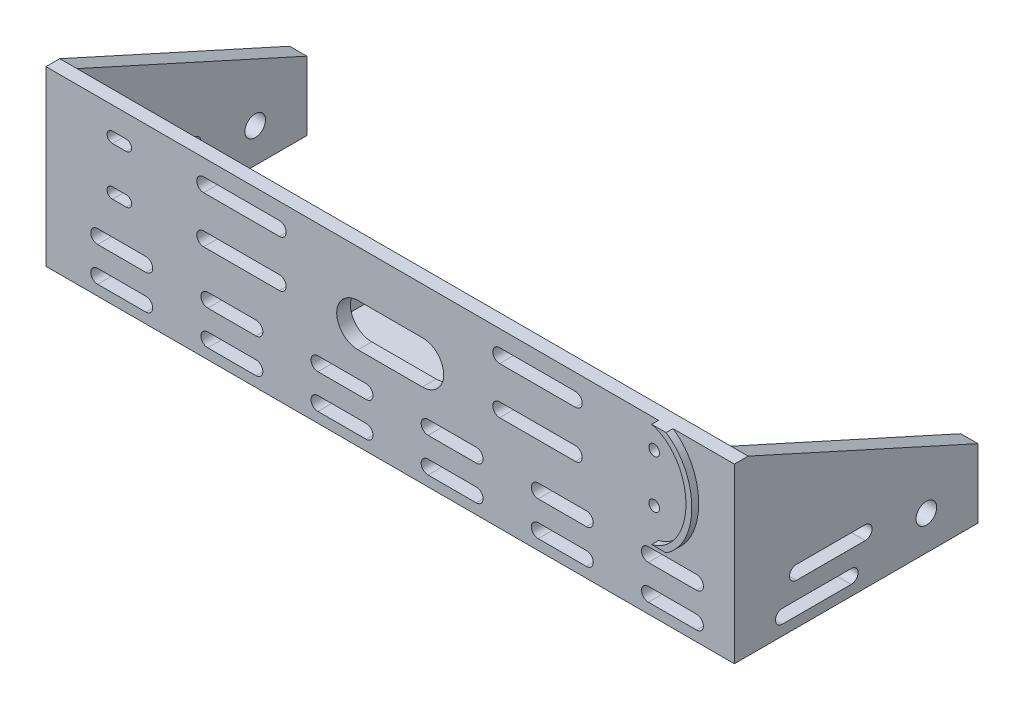
SolidWorks part; units mm, degrees
ref_plane "前视基准面" through (0, 0, 0) normal (0, 0, 1) x (1, 0, 0)
ref_plane "上视基准面" through (0, 0, 0) normal (0, 1, 0) x (1, 0, 0)
ref_plane "右视基准面" through (0, 0, 0) normal (1, 0, 0) x (0, 0, -1)
sketch "草图1" plane through (0, 0, 0) normal (0, 0, 1) x (1, 0, 0)
  line L1 (-100, 100) -> (100, 100)
  line L2 (-100, 100) -> (-100, -100)
  line L3 (-100, -100) -> (100, -100)
  line L4 (100, 100) -> (100, -100)
  line L5 (-100, 100) -> (100, -100) construction
  line L6 (-100, -100) -> (100, 100) construction
  point P0 (0, 0)
extrude "凸台-拉伸1" add sketch "草图1" along normal blind 4
sketch "草图2" plane through (0, 0, 4) normal (0, 0, 1) x (1, 0, 0)
  line L2 (-72.6076, -10.5305) -> (78.3924, -10.5305)
  line L3 (-72.6076, 19.72) -> (78.3924, 19.72)
  line L12 (100, -100) -> (100, 100)
  line L13 (100, 100) -> (-100, 100)
  line L14 (-100, 100) -> (-100, -100)
  line L15 (-100, -100) -> (100, -100)
  line L16 (100, -100) -> (100, 100)
  line L17 (100, 100) -> (-100, 100)
  line L18 (-100, 100) -> (-100, -100)
  line L19 (-100, -100) -> (100, -100)
  spline S4 degree 3 number of poles 131 (78.3924, -10.5305) -> (78.3924, 19.72)
  spline S6 degree 3 number of poles 138 (-72.6076, 19.72) -> (-72.6076, -10.5305)
  dimension "D1" = 0
extrude "切除-拉伸1" cut sketch "草图2" against normal blind 10
sketch "草图3" plane through (0, 0, 0) normal (0, 0, -1) x (-1, 0, 0)
  line L5 (-12.2424, -6.2053) -> (6.4576, -6.2053)
  line L6 (6.4576, 6.1947) -> (-12.2424, 6.1947)
  arc A6 (6.4576, -6.2053) -> (6.4576, 6.1947) centre (6.4576, -0.0053) ccw
  arc A7 (-12.2424, 6.1947) -> (-12.2424, -6.2053) centre (-12.2424, -0.0053) ccw
extrude "切除-拉伸2" cut sketch "草图3" against normal blind 10
sketch "草图4" plane through (0, 0, 0) normal (0, 0, -1) x (-1, 0, 0)
  circle A1 centre (-79.5924, 11.5947) radius 1.2645
  circle A3 centre (-79.5924, -2.4053) radius 1.2645
  circle A5 centre (73.8076, 11.5947) radius 1.2645
  circle A7 centre (73.8076, -2.4053) radius 1.2645
extrude "切除-拉伸3" cut sketch "草图4" against normal blind 10
sketch "草图5" plane through (0, 0, 0) normal (0, 0, -1) x (-1, 0, 0)
  circle A4 centre (73.8076, -2.4053) radius 1.2645 construction
  circle A5 centre (73.8076, -2.4053) radius 1.2645
  circle A6 centre (73.8076, 11.5947) radius 1.2645 construction
  circle A7 centre (73.8076, 11.5947) radius 1.2645
  circle A8 centre (73.8076, 11.5947) radius 1.5645
  circle A9 centre (73.8076, -2.4053) radius 1.5645
  circle A10 centre (-79.5924, -2.4053) radius 1.5645
  circle A11 centre (-79.5924, 11.5947) radius 1.5645
  dimension "D1" = 0.3
extrude "切除-拉伸4" cut sketch "草图5" against normal blind 10
sketch "草图6" plane through (0, 0, 0) normal (0, 0, -1) x (-1, 0, 0)
  line L0 (-78.3924, -10.5305) -> (-78.3924, -7.5305)
  line L1 (72.6076, -10.5305) -> (-78.3924, -10.5305) construction
  line L2 (-78.3924, -7.5305) -> (72.6076, -7.5305)
  line L3 (72.6076, -7.5305) -> (72.6076, -10.5305)
  line L4 (72.6076, -10.5305) -> (-78.3924, -10.5305)
  spline S0 degree 3 number of poles 138 (72.6076, 19.72) -> (72.6076, -10.5305) construction
extrude "凸台-拉伸2" add sketch "草图6" along normal blind 25
sketch "草图7" plane through (0, -7.5305, 0) normal (0, 1, 0) x (1, 0, 0)
  line L0 (23.6853, 0) -> (25.6853, 0)
  line L1 (-72.6076, 25) -> (78.3924, 25) construction
  line L2 (-72.6076, 0) -> (78.3924, 0) construction
  line L3 (67.6853, 25) -> (67.6853, 0)
  line L4 (69.6853, 25) -> (69.6853, 0)
  line L5 (67.6853, 0) -> (69.6853, 0)
  line L6 (67.6853, 25) -> (69.6853, 25)
  line L7 (25.6853, 25) -> (25.6853, 0)
  line L8 (23.6853, 25) -> (25.6853, 25)
  line L9 (23.6853, 25) -> (23.6853, 0)
  line L10 (-20.3147, 0) -> (-18.3147, 0)
  line L11 (-18.3147, 25) -> (-18.3147, 0)
  line L12 (-20.3147, 25) -> (-18.3147, 25)
  line L13 (-20.3147, 25) -> (-20.3147, 0)
  line L14 (-64.3147, 0) -> (-62.3147, 0)
  line L15 (-62.3147, 25) -> (-62.3147, 0)
  line L16 (-64.3147, 25) -> (-62.3147, 25)
  line L17 (-64.3147, 25) -> (-64.3147, 0)
  dimension "D1" = 4
extrude "凸台-拉伸3" add sketch "草图7" along normal up to surface (27.2505 mm away) contours L5 L4 L6 L3 | L0 L7 L8 L9 | L10 L11 L12 L13 | L14 L15 L16 L17 up to face at (2.8924, 19.72, 2)
sketch "草图8" plane through (69.6853, 0, 0) normal (1, 0, 0) x (0, 0, -1)
  line L0 (0, 19.72) -> (25, -7.5305)
  line L1 (25, 19.72) -> (25, -7.5305) construction
  line L2 (25, -7.5305) -> (25, 19.72)
  line L3 (25, 19.72) -> (0, 19.72) construction
  line L4 (25, 19.72) -> (0, 19.72)
extrude "切除-拉伸5" cut sketch "草图8" against normal through all
sketch "草图9" plane through (78.3924, 0, 0) normal (1, 0, 0) x (0, 0, -1)
  line L4 (0, -7.5305) -> (0, -10.5305)
  line L5 (0, -10.5305) -> (25, -10.5305)
  line L6 (25, -10.5305) -> (25, -7.5305)
  line L7 (25, -7.5305) -> (0, -7.5305)
  line L8 (0, -7.5305) -> (0, -10.5305)
  line L9 (0, -10.5305) -> (25, -10.5305)
  line L10 (25, -10.5305) -> (25, -7.5305)
  line L11 (25, -7.5305) -> (0, -7.5305)
  dimension "D1" = 0
extrude "凸台-拉伸4" add sketch "草图9" along normal blind 19.5
sketch "草图10" plane through (-72.6076, 0, 0) normal (-1, 0, 0) x (0, 0, 1)
  line L4 (0, -10.5305) -> (0, -7.5305)
  line L5 (0, -7.5305) -> (-25, -7.5305)
  line L6 (-25, -7.5305) -> (-25, -10.5305)
  line L7 (-25, -10.5305) -> (0, -10.5305)
  line L8 (0, -10.5305) -> (0, -7.5305)
  line L9 (0, -7.5305) -> (-25, -7.5305)
  line L10 (-25, -7.5305) -> (-25, -10.5305)
  line L11 (-25, -10.5305) -> (0, -10.5305)
  dimension "D1" = 0
extrude "凸台-拉伸5" add sketch "草图10" along normal blind 19.5
sketch "草图11" plane through (0, 0, 0) normal (0, 0, -1) x (-1, 0, 0)
  line L3 (-85.6613, -7.5305) -> (-69.6853, -7.5305)
  line L4 (-69.6853, -7.5305) -> (-69.6853, 19.72)
  line L5 (-69.6853, 19.72) -> (-78.3924, 19.72)
  line L6 (-85.6613, -7.5305) -> (-69.6853, -7.5305)
  line L7 (-69.6853, -7.5305) -> (-69.6853, 19.72)
  line L8 (-69.6853, 19.72) -> (-78.3924, 19.72)
  line L9 (64.3147, -7.5305) -> (79.8759, -7.5305)
  line L10 (72.6076, 19.72) -> (64.3147, 19.72)
  line L11 (64.3147, 19.72) -> (64.3147, -7.5305)
  line L12 (64.3147, -7.5305) -> (79.8759, -7.5305)
  line L13 (72.6076, 19.72) -> (64.3147, 19.72)
  line L14 (64.3147, 19.72) -> (64.3147, -7.5305)
  line L16 (72.6076, 19.72) -> (92.1076, 19.72)
  line L17 (92.1076, 19.72) -> (92.1076, -7.5305)
  line L18 (-97.8924, -7.5305) -> (-97.8924, 19.72)
  line L19 (-97.8924, 19.72) -> (-78.3924, 19.72)
  line L20 (92.1076, -10.5305) -> (72.6076, -10.5305) construction
  line L21 (92.1076, -10.5305) -> (72.6076, -10.5305)
  line L22 (92.1076, -10.5305) -> (92.1076, -7.5305) construction
  line L23 (92.1076, -10.5305) -> (92.1076, -7.5305)
  line L24 (-97.8924, -10.5305) -> (-78.3924, -10.5305) construction
  line L25 (-97.8924, -10.5305) -> (-78.3924, -10.5305)
  line L26 (-97.8924, -7.5305) -> (-97.8924, -10.5305) construction
  line L27 (-97.8924, -7.5305) -> (-97.8924, -10.5305)
  circle A0 centre (-79.5924, 11.5947) radius 1.5645 construction
  circle A1 centre (-79.5924, 11.5947) radius 1.5645
  circle A2 centre (-79.5924, -2.4053) radius 1.5645 construction
  circle A3 centre (-79.5924, -2.4053) radius 1.5645
  circle A4 centre (73.8076, 11.5947) radius 1.5645 construction
  circle A5 centre (73.8076, 11.5947) radius 1.5645
  circle A6 centre (73.8076, -2.4053) radius 1.5645 construction
  circle A7 centre (73.8076, -2.4053) radius 1.5645
  spline S0 degree 3 poles (-1964.2663, -2201.2134) (52.8845, 109.7009) (102.2719, 11.1981) (79.208, -8.1129) (78.9676, -8.2994) (78.6552, -8.5321) (78.2893, -8.7882) (77.9099, -9.0221) (77.6333, -9.182) (77.5386, -9.2349) (77.2976, -9.3648) (76.9963, -9.5185) (76.6866, -9.6585) (76.3996, -9.7797) (76.1261, -9.889) (75.7015, -10.0382) (75.4033, -10.1279) (75.1767, -10.1905) (75.0211, -10.2315) (74.7914, -10.2863) (74.561, -10.3356) (74.3307, -10.3792) (74.0991, -10.4175) (73.8974, -10.446) (73.6934, -10.4708) (73.4878, -10.4919) (73.2229, -10.5125) (72.9576, -10.5256) (72.7484, -10.5299) (72.6472, -10.5304) (72.6264, -10.5305) (71.9929, -10.5316) (65.2261, -10.4746) (3070.0625, -10.2829) knots -0.052986 -0.052986 -0.052986 -0.052986 0.035105 0.035549 0.036008 0.036008 0.03671 0.037341 0.037341 0.037666 0.037666 0.038159 0.038675 0.038675 0.039081 0.039546 0.040009 0.040009 0.040249 0.0405 0.040755 0.04101 0.041263 0.041513 0.041655 0.041897 0.042132 0.042414 0.042612 0.04266 0.04266 0.042662 0.044149 0.044149 0.044149 0.044149 weights 1 1 1 1 1 1 1 1 1 1 1 1 1 1 1 1 1 1 1 1 1 1 1 1 1 1 1 1 1 1 1 1 1 1 only from (79.8759, -7.5305) to (72.6076, -10.5305) construction
  spline S1 degree 3 number of poles 100 (-78.3924, 19.72) -> (-85.6613, -7.5305)
  spline S2 degree 3 poles (79.8759, -7.5305) (79.7709, -7.6281) (79.5523, -7.8246) (79.208, -8.1129) (78.9676, -8.2994) (78.6552, -8.5321) (78.2893, -8.7882) (77.9099, -9.0221) (77.6333, -9.182) (77.5386, -9.2349) (77.2976, -9.3648) (76.9963, -9.5185) (76.6866, -9.6585) (76.3996, -9.7797) (76.1261, -9.889) (75.7015, -10.0382) (75.4033, -10.1279) (75.1767, -10.1905) (75.0211, -10.2315) (74.7914, -10.2863) (74.561, -10.3356) (74.3307, -10.3792) (74.0991, -10.4175) (73.8974, -10.446) (73.6934, -10.4708) (73.4878, -10.4919) (73.2229, -10.5125) (72.9576, -10.5256) (72.7484, -10.5299) (72.6472, -10.5304) (72.6264, -10.5305) (72.6196, -10.5305) (72.6122, -10.5305) (72.6076, -10.5305) knots 0.034679 0.034679 0.034679 0.034679 0.035105 0.035549 0.036008 0.036008 0.03671 0.037341 0.037341 0.037666 0.037666 0.038159 0.038675 0.038675 0.039081 0.039546 0.040009 0.040009 0.040249 0.0405 0.040755 0.04101 0.041263 0.041513 0.041655 0.041897 0.042132 0.042414 0.042612 0.04266 0.04266 0.042662 0.042676 0.042676 0.042676 0.042676 weights 1 1 1 1 1 1 1 1 1 1 1 1 1 1 1 1 1 1 1 1 1 1 1 1 1 1 1 1 1 1 1 1 1 1
  spline S3 degree 3 number of poles 107 (79.8759, -7.5305) -> (72.6076, 19.72)
  spline S4 degree 3 poles (-3072.7814, -10.217) (-88.9792, -10.474) (-77.7118, -10.5313) (-78.4074, -10.5305) (-78.4599, -10.5304) (-78.5623, -10.5294) (-78.7097, -10.5257) (-78.8675, -10.5194) (-79.0115, -10.5113) (-79.1631, -10.5005) (-79.3142, -10.4875) (-79.4815, -10.4703) (-79.6251, -10.4531) (-79.7145, -10.4411) (-79.8286, -10.4253) (-80.0633, -10.3896) (-80.448, -10.3171) (-80.8046, -10.2327) (-81.0101, -10.1772) (-81.2711, -10.1043) (-81.6531, -9.9845) (-82.205, -9.7759) (-82.7332, -9.5427) (-83.0804, -9.3664) (-83.3635, -9.2127) (-83.5947, -9.0822) (-83.9446, -8.8678) (-84.3033, -8.629) (-84.5366, -8.4609) (-84.6781, -8.355) (-84.8686, -8.2112) (-133.4278, 30.7748) (133.5555, 417.232) (-2378.5676, -1932.7537) knots -0.001469 -0.001469 -0.001469 -0.001469 0.000004 0.000016 0.000016 0.000132 0.000273 0.000411 0.000581 0.000707 0.000886 0.001066 0.001245 0.001336 0.001336 0.001585 0.002038 0.002493 0.002673 0.002673 0.003304 0.003874 0.004447 0.005039 0.005039 0.005408 0.005829 0.006254 0.006682 0.006682 0.00678 0.007394 0.192748 0.192748 0.192748 0.192748 weights 1 1 1 1 1 1 1 1 1 1 1 1 1 1 1 1 1 1 1 1 1 1 1 1 1 1 1 1 1 1 1 1 1 1 only from (-78.3924, -10.5305) to (-85.6613, -7.5305) construction
  spline S5 degree 3 poles (-78.3924, -10.5305) (-78.3939, -10.5305) (-78.4, -10.5305) (-78.4074, -10.5305) (-78.4599, -10.5304) (-78.5623, -10.5294) (-78.7097, -10.5257) (-78.8675, -10.5194) (-79.0115, -10.5113) (-79.1631, -10.5005) (-79.3142, -10.4875) (-79.4815, -10.4703) (-79.6251, -10.4531) (-79.7145, -10.4411) (-79.8286, -10.4253) (-80.0633, -10.3896) (-80.448, -10.3171) (-80.8046, -10.2327) (-81.0101, -10.1772) (-81.2711, -10.1043) (-81.6531, -9.9845) (-82.205, -9.7759) (-82.7332, -9.5427) (-83.0804, -9.3664) (-83.3635, -9.2127) (-83.5947, -9.0822) (-83.9446, -8.8678) (-84.3033, -8.629) (-84.5366, -8.4609) (-84.6781, -8.355) (-84.8686, -8.2112) (-85.211, -7.9363) (-85.5144, -7.6671) (-85.6613, -7.5305) knots 0 0 0 0 0.000004 0.000016 0.000016 0.000132 0.000273 0.000411 0.000581 0.000707 0.000886 0.001066 0.001245 0.001336 0.001336 0.001585 0.002038 0.002493 0.002673 0.002673 0.003304 0.003874 0.004447 0.005039 0.005039 0.005408 0.005829 0.006254 0.006682 0.006682 0.00678 0.007394 0.007994 0.007994 0.007994 0.007994 weights 1 1 1 1 1 1 1 1 1 1 1 1 1 1 1 1 1 1 1 1 1 1 1 1 1 1 1 1 1 1 1 1 1 1
  dimension "D1" = 0
  dimension "D2" = 0
extrude "凸台-拉伸7" add sketch "草图11" against normal up to surface (4 mm away) up to face at (81.1569, 11.5947, 4)
sketch "草图12" plane through (97.8924, 0, 0) normal (1, 0, 0) x (0, 0, -1)
  line L0 (0, 19.72) -> (0, -7.5305)
  line L1 (0, 19.72) -> (0, -7.5305) construction
  line L2 (-4, 19.72) -> (0, 19.72) construction
  line L3 (25, -7.5305) -> (0, -7.5305) construction
  line L4 (0, -7.5305) -> (25, -7.5305)
  line L5 (25, -7.5305) -> (25, 19.72)
  line L6 (25, 19.72) -> (0, 19.72)
extrude "凸台-拉伸8" add sketch "草图12" against normal blind 2
sketch "草图13" plane through (-92.1076, 0, 0) normal (-1, 0, 0) x (0, 0, 1)
  line L0 (-25, -7.5305) -> (0, -7.5305)
  line L1 (0, -7.5305) -> (-25, -7.5305) construction
  line L2 (0, -7.5305) -> (0, 19.72) construction
  line L3 (0, -7.5305) -> (0, 19.72)
  line L4 (4, 19.72) -> (0, 19.72) construction
  line L5 (0, 19.72) -> (-25, 19.72)
  line L6 (-25, 19.72) -> (-25, -7.5305)
extrude "凸台-拉伸9" add sketch "草图13" against normal blind 2
sketch "草图14" plane through (97.8924, 0, 0) normal (1, 0, 0) x (0, 0, -1)
  line L0 (0, 19.72) -> (25, -7.5305) construction
  line L1 (0, 19.72) -> (25, -7.5305)
  line L2 (-4, 19.72) -> (25, 19.72) construction
  line L3 (0, 19.72) -> (25, 19.72)
  line L4 (25, -10.5305) -> (25, 19.72) construction
  line L5 (25, -7.5305) -> (25, 19.72)
extrude "切除-拉伸6" cut sketch "草图14" against normal through all
sketch "草图15" plane through (0, 0, 4) normal (0, 0, 1) x (1, 0, 0)
  line L1 (97.8924, 19.72) -> (-92.1076, 19.72) construction
  line L3 (-79.2671, 19.72) -> (-75.0584, 19.72)
  line L6 (2.8924, 19.72) -> (2.8924, 11.147) construction
  line L7 (80.8432, -10.5305) -> (85.0515, -10.5305)
  line L10 (-92.1076, -10.5305) -> (97.8924, -10.5305) construction
  line L11 (-79.2668, -10.5305) -> (-75.0584, -10.5305)
  line L15 (85.0518, 19.72) -> (80.8432, 19.72)
  spline S0 degree 3 poles (85.0518, 19.72) (85.1632, 19.6484) (85.4315, 19.4703) (86.1206, 18.9769) (87.4522, 17.859) (89.1534, 15.8951) (90.6757, 13.2854) (92.1095, 9.5189) (92.7901, 4.6117) (91.9718, -1.3231) (89.8146, -5.9461) (87.3308, -8.8099) (85.859, -9.9966) (85.1617, -10.4597) (85.0515, -10.5305) knots 0.005857 0.005857 0.005857 0.005857 0.006191 0.006668 0.008002 0.010669 0.013336 0.016003 0.021338 0.026672 0.032007 0.034674 0.036473 0.036807 0.036807 0.036807 0.036807
  spline S1 degree 3 poles (-75.0584, 19.72) (-75.1603, 19.6948) (-75.7066, 19.5507) (-76.6676, 19.2127) (-77.8948, 18.5992) (-79.0593, 17.8276) (-80.4578, 16.6538) (-82.5778, 14.2113) (-84.5252, 10.0319) (-85.2857, 4.6081) (-84.5294, -0.8444) (-82.5636, -5.0408) (-80.1537, -7.815) (-78.2999, -9.2065) (-76.6615, -10.0277) (-75.6724, -10.3713) (-75.1497, -10.508) (-75.0584, -10.5305) knots 0.002364 0.002364 0.002364 0.002364 0.002667 0.004001 0.005334 0.006668 0.008002 0.010669 0.016003 0.021338 0.026672 0.032007 0.034674 0.037341 0.038675 0.040009 0.040293 0.040293 0.040293 0.040293
  spline S2 degree 3 poles (80.8432, 19.72) (80.9451, 19.6948) (81.4914, 19.5507) (82.4524, 19.2127) (83.6795, 18.5992) (84.844, 17.8276) (86.2425, 16.6538) (88.3625, 14.2113) (90.3099, 10.0319) (91.0705, 4.6081) (90.3141, -0.8444) (88.3483, -5.0408) (85.9384, -7.815) (84.0847, -9.2065) (82.4463, -10.0277) (81.4571, -10.3713) (80.9345, -10.508) (80.8432, -10.5305) knots 0.002364 0.002364 0.002364 0.002364 0.002667 0.004001 0.005334 0.006668 0.008002 0.010669 0.016003 0.021338 0.026672 0.032007 0.034674 0.037341 0.038675 0.040009 0.040293 0.040293 0.040293 0.040293
  spline S7 degree 3 poles (-79.2671, 19.72) (-79.3785, 19.6484) (-79.6467, 19.4703) (-80.3358, 18.9769) (-81.6674, 17.859) (-83.3686, 15.8951) (-84.891, 13.2854) (-86.3248, 9.5189) (-87.0054, 4.6117) (-86.1871, -1.3231) (-84.0298, -5.9461) (-81.5461, -8.8099) (-80.0742, -9.9966) (-79.3769, -10.4597) (-79.2668, -10.5305) knots 0.005857 0.005857 0.005857 0.005857 0.006191 0.006668 0.008002 0.010669 0.013336 0.016003 0.021338 0.026672 0.032007 0.034674 0.036473 0.036807 0.036807 0.036807 0.036807
extrude "凸台-拉伸10" add sketch "草图15" along normal blind 2
sketch "草图17" plane through (97.8924, 0, 0) normal (1, 0, 0) x (0, 0, -1)
  line L1 (66.7816, -30.5305) -> (66.7816, -10.5305)
  line L2 (25, -10.5305) -> (66.7816, -10.5305)
  line L3 (-4, -10.5305) -> (25, -10.5305) construction
  line L4 (-4, 19.72) -> (-4, -10.5305) construction
  line L5 (-4, -10.5305) -> (-4, -30.5305)
  line L6 (-4, -30.5305) -> (66.7816, -30.5305)
  line L12 (25, -7.5305) -> (0, 19.72)
  line L13 (0, 19.72) -> (-4, 19.72)
  line L14 (-4, 19.72) -> (-4, -10.5305)
  line L15 (-4, -10.5305) -> (25, -10.5305)
  line L16 (25, -10.5305) -> (25, -7.5305)
  line L17 (25, -7.5305) -> (0, 19.72)
  line L18 (0, 19.72) -> (-4, 19.72)
  line L19 (-4, 19.72) -> (-4, -10.5305)
  line L21 (25, -10.5305) -> (25, -7.5305)
  dimension "D1" = 0
extrude "凸台-拉伸11" add sketch "草图17" along normal blind 5
sketch "草图18" plane through (102.8924, 0, 0) normal (1, 0, 0) x (0, 0, -1)
  line L1 (36.7816, -30.5305) -> (36.7816, -10.5305) construction
  line L2 (66.7816, -10.5305) -> (25, -10.5305) construction
  line L3 (66.7816, -10.5305) -> (36.7816, -10.5305) construction
  line L4 (66.7816, -10.5305) -> (66.7816, -30.5305) construction
  line L5 (66.7816, -30.5305) -> (36.7816, -30.5305) construction
  line L6 (-4, -30.5305) -> (66.7816, -30.5305) construction
  line L7 (36.7816, -20.5305) -> (66.7816, -20.5305) construction
  circle A0 centre (51.7816, -20.5305) radius 3
extrude "切除-拉伸7" cut sketch "草图18" against normal through all
ref_plane "基准面1" through (2.8924, 0, 0) normal (-1, 0, 0) x (0, 0, 1)
mirror "镜向1" about plane through (2.8924, 0, 0) normal (-1, 0, 0) of "凸台-拉伸11", "切除-拉伸7"
sketch "草图19" plane through (102.8924, 0, 0) normal (1, 0, 0) x (0, 0, -1)
  line L0 (0, 19.72) -> (66.7816, -10.5305)
  line L1 (66.7816, -10.5305) -> (25, -10.5305)
  line L2 (25, -10.5305) -> (25, -7.5305)
  line L3 (25, -10.5305) -> (25, -7.5305) construction
  line L4 (25, -7.5305) -> (0, 19.72) construction
  line L5 (25, -7.5305) -> (0, 19.72)
extrude "凸台-拉伸12" add sketch "草图19" against normal up to surface (5 mm away) up to face at (97.8924, -20.5305, -54.7816)
sketch "草图20" plane through (-97.1076, 0, 0) normal (-1, 0, 0) x (0, 0, 1)
  line L0 (-66.7816, -10.5305) -> (0, 19.72)
  line L1 (0, 19.72) -> (-25, -7.5305)
  line L2 (-25, -7.5305) -> (-25, -10.5305)
  line L3 (-25, -10.5305) -> (-25, -7.5305) construction
  line L4 (-66.7816, -10.5305) -> (-25, -10.5305) construction
  line L5 (-25, -10.5305) -> (-66.7816, -10.5305)
extrude "凸台-拉伸13" add sketch "草图20" against normal up to surface (5 mm away) up to face at (-92.1076, -20.5305, -48.7816)
sketch "草图21" plane through (0, 0, 0) normal (0, 0, -1) x (-1, 0, 0)
  line L0 (-67.6853, 6.0947) -> (-23.6853, 6.0947) construction
  line L1 (-67.6853, 19.72) -> (-67.6853, -7.5305) construction
  line L2 (-23.6853, 19.72) -> (-23.6853, -7.5305) construction
  line L3 (-45.6853, 6.0947) -> (-45.6853, 19.72) construction
  line L4 (-67.6853, 19.72) -> (-25.6853, 19.72) construction
  line L5 (-45.6853, 12.9074) -> (-67.6853, 12.9074) construction
  line L6 (-56.6853, 12.9074) -> (-34.6853, 12.9074) construction
  line L7 (-23.6853, 19.72) -> (18.3147, 19.72) construction
  line L8 (-56.6853, 14.9074) -> (-34.6853, 14.9074)
  line L9 (-56.6853, 10.9074) -> (-34.6853, 10.9074)
  line L10 (-23.6853, 19.72) -> (18.3147, 19.72) construction
  line L11 (-2.6853, 19.72) -> (-2.6853, 9.3359) construction
  line L12 (-56.6853, -0.7179) -> (-34.6853, -0.7179) construction
  line L13 (-56.6853, -2.7179) -> (-34.6853, -2.7179)
  line L14 (-56.6853, 1.2821) -> (-34.6853, 1.2821)
  line L15 (51.3147, -0.7179) -> (29.3147, -0.7179) construction
  line L16 (51.3147, -2.7179) -> (29.3147, -2.7179)
  line L17 (51.3147, 1.2821) -> (29.3147, 1.2821)
  line L18 (51.3147, 12.9074) -> (29.3147, 12.9074) construction
  line L19 (51.3147, 14.9074) -> (29.3147, 14.9074)
  line L20 (51.3147, 10.9074) -> (29.3147, 10.9074)
  arc A0 (-56.6853, 14.9074) -> (-56.6853, 10.9074) centre (-56.6853, 12.9074) ccw
  arc A1 (-34.6853, 10.9074) -> (-34.6853, 14.9074) centre (-34.6853, 12.9074) ccw
  arc A2 (-56.6853, -2.7179) -> (-56.6853, 1.2821) centre (-56.6853, -0.7179) cw
  arc A3 (-34.6853, 1.2821) -> (-34.6853, -2.7179) centre (-34.6853, -0.7179) cw
  arc A4 (51.3147, -2.7179) -> (51.3147, 1.2821) centre (51.3147, -0.7179) ccw
  arc A5 (29.3147, 1.2821) -> (29.3147, -2.7179) centre (29.3147, -0.7179) ccw
  arc A6 (51.3147, 14.9074) -> (51.3147, 10.9074) centre (51.3147, 12.9074) cw
  arc A7 (29.3147, 10.9074) -> (29.3147, 14.9074) centre (29.3147, 12.9074) cw
  point P16 (-45.6853, 12.9074)
  point P25 (-45.6853, -0.7179)
  point P32 (40.3147, -0.7179)
  point P39 (40.3147, 12.9074)
extrude "切除-拉伸8" cut sketch "草图21" against normal blind 4
sketch "草图22" plane through (102.8924, 0, 0) normal (1, 0, 0) x (0, 0, -1)
  line L0 (23.8908, -20.5305) -> (-4, -20.5305) construction
  line L1 (-4, 19.72) -> (-4, -30.5305) construction
  line L2 (23.8908, -20.5305) -> (23.8908, -30.5305) construction
  line L3 (-4, -30.5305) -> (66.7816, -30.5305) construction
  line L4 (9.9454, -20.5305) -> (9.9454, -30.5305) construction
  line L5 (9.9454, -25.5305) -> (29.9454, -25.5305) construction
  line L6 (19.9454, -25.5305) -> (33.3908, 4.5947) construction
  line L7 (9.9454, -23.5305) -> (29.9454, -23.5305)
  line L8 (9.9454, -27.5305) -> (29.9454, -27.5305)
  line L9 (66.7816, -10.5305) -> (0, 19.72) construction
  line L10 (9.9454, -25.5305) -> (25.2598, 8.2779) construction
  line L11 (29.9454, -25.5305) -> (41.8547, 0.7608) construction
  line L12 (14.0175, -16.5408) -> (34.0175, -16.5408) construction
  line L13 (14.0175, -14.5408) -> (34.0175, -14.5408)
  line L14 (14.0175, -18.5408) -> (34.0175, -18.5408)
  arc A0 (9.9454, -23.5305) -> (9.9454, -27.5305) centre (9.9454, -25.5305) ccw
  arc A1 (29.9454, -27.5305) -> (29.9454, -23.5305) centre (29.9454, -25.5305) ccw
  arc A2 (14.0175, -14.5408) -> (14.0175, -18.5408) centre (14.0175, -16.5408) ccw
  arc A3 (34.0175, -18.5408) -> (34.0175, -14.5408) centre (34.0175, -16.5408) ccw
  point P14 (19.9454, -25.5305)
  point P26 (24.0175, -16.5408)
extrude "切除-拉伸9" cut sketch "草图22" against normal through all
sketch "草图23" plane through (97.8924, 0, 0) normal (-1, 0, 0) x (0, 0, 1)
  line L0 (4, -30.5305) -> (0, -30.5305)
  line L1 (4, -30.5305) -> (-66.7816, -30.5305) construction
  line L2 (0, -30.5305) -> (0, -10.5305)
  line L3 (4, -10.5305) -> (-25, -10.5305) construction
  line L4 (0, -10.5305) -> (4, -10.5305)
  line L5 (4, -10.5305) -> (4, -30.5305)
extrude "凸台-拉伸14" add sketch "草图23" along normal up to surface (190 mm away)
sketch "草图24" plane through (0, 0, 4) normal (0, 0, 1) x (1, 0, 0)
  line L0 (-82.1076, -25.5305) -> (-68.1076, -25.5305) construction
  line L2 (-92.1076, -20.5305) -> (-92.1076, -30.5305) construction
  line L3 (102.8924, -30.5305) -> (-97.1076, -30.5305) construction
  line L4 (-92.1076, -30.5305) -> (97.8924, -30.5305) construction
  line L5 (97.8924, -30.5305) -> (97.8924, -20.5305) construction
  line L6 (-92.1076, -20.5305) -> (97.8924, -20.5305) construction
  line L7 (-92.1076, -25.5305) -> (-82.1076, -25.5305) construction
  line L8 (-82.1076, -15.5305) -> (-68.1076, -15.5305) construction
  line L9 (-82.1076, -23.5305) -> (-68.1076, -23.5305)
  line L10 (-82.1076, -27.5305) -> (-68.1076, -27.5305)
  line L11 (-82.1076, -17.5305) -> (-68.1076, -17.5305)
  line L12 (-82.1076, -13.5305) -> (-68.1076, -13.5305)
  line L13 (-50.1076, -25.5305) -> (-36.1076, -25.5305) construction
  line L14 (-50.1076, -23.5305) -> (-36.1076, -23.5305)
  line L15 (-50.1076, -27.5305) -> (-36.1076, -27.5305)
  line L16 (-50.1076, -15.5305) -> (-36.1076, -15.5305) construction
  line L17 (-50.1076, -17.5305) -> (-36.1076, -17.5305)
  line L18 (-50.1076, -13.5305) -> (-36.1076, -13.5305)
  line L19 (-18.1076, -25.5305) -> (-4.1076, -25.5305) construction
  line L20 (-18.1076, -23.5305) -> (-4.1076, -23.5305)
  line L21 (-18.1076, -27.5305) -> (-4.1076, -27.5305)
  line L22 (-18.1076, -15.5305) -> (-4.1076, -15.5305) construction
  line L23 (-18.1076, -17.5305) -> (-4.1076, -17.5305)
  line L24 (-18.1076, -13.5305) -> (-4.1076, -13.5305)
  line L25 (13.8924, -25.5305) -> (27.8924, -25.5305) construction
  line L26 (13.8924, -23.5305) -> (27.8924, -23.5305)
  line L27 (13.8924, -27.5305) -> (27.8924, -27.5305)
  line L28 (13.8924, -15.5305) -> (27.8924, -15.5305) construction
  line L29 (13.8924, -17.5305) -> (27.8924, -17.5305)
  line L30 (13.8924, -13.5305) -> (27.8924, -13.5305)
  line L31 (45.8924, -25.5305) -> (59.8924, -25.5305) construction
  line L32 (45.8924, -23.5305) -> (59.8924, -23.5305)
  line L33 (45.8924, -27.5305) -> (59.8924, -27.5305)
  line L34 (45.8924, -15.5305) -> (59.8924, -15.5305) construction
  line L35 (45.8924, -17.5305) -> (59.8924, -17.5305)
  line L36 (45.8924, -13.5305) -> (59.8924, -13.5305)
  line L37 (77.8924, -25.5305) -> (91.8924, -25.5305) construction
  line L38 (77.8924, -23.5305) -> (91.8924, -23.5305)
  line L39 (77.8924, -27.5305) -> (91.8924, -27.5305)
  line L40 (77.8924, -15.5305) -> (91.8924, -15.5305) construction
  line L41 (77.8924, -17.5305) -> (91.8924, -17.5305)
  line L42 (77.8924, -13.5305) -> (91.8924, -13.5305)
  arc A0 (-82.1076, -23.5305) -> (-82.1076, -27.5305) centre (-82.1076, -25.5305) ccw
  arc A1 (-68.1076, -27.5305) -> (-68.1076, -23.5305) centre (-68.1076, -25.5305) ccw
  arc A2 (-82.1076, -17.5305) -> (-82.1076, -13.5305) centre (-82.1076, -15.5305) cw
  arc A3 (-68.1076, -13.5305) -> (-68.1076, -17.5305) centre (-68.1076, -15.5305) cw
  arc A4 (-50.1076, -23.5305) -> (-50.1076, -27.5305) centre (-50.1076, -25.5305) ccw
  arc A5 (-36.1076, -27.5305) -> (-36.1076, -23.5305) centre (-36.1076, -25.5305) ccw
  arc A6 (-50.1076, -17.5305) -> (-50.1076, -13.5305) centre (-50.1076, -15.5305) cw
  arc A7 (-36.1076, -13.5305) -> (-36.1076, -17.5305) centre (-36.1076, -15.5305) cw
  arc A8 (-18.1076, -23.5305) -> (-18.1076, -27.5305) centre (-18.1076, -25.5305) ccw
  arc A9 (-4.1076, -27.5305) -> (-4.1076, -23.5305) centre (-4.1076, -25.5305) ccw
  arc A10 (-18.1076, -17.5305) -> (-18.1076, -13.5305) centre (-18.1076, -15.5305) cw
  arc A11 (-4.1076, -13.5305) -> (-4.1076, -17.5305) centre (-4.1076, -15.5305) cw
  arc A12 (13.8924, -23.5305) -> (13.8924, -27.5305) centre (13.8924, -25.5305) ccw
  arc A13 (27.8924, -27.5305) -> (27.8924, -23.5305) centre (27.8924, -25.5305) ccw
  arc A14 (13.8924, -17.5305) -> (13.8924, -13.5305) centre (13.8924, -15.5305) cw
  arc A15 (27.8924, -13.5305) -> (27.8924, -17.5305) centre (27.8924, -15.5305) cw
  arc A16 (45.8924, -23.5305) -> (45.8924, -27.5305) centre (45.8924, -25.5305) ccw
  arc A17 (59.8924, -27.5305) -> (59.8924, -23.5305) centre (59.8924, -25.5305) ccw
  arc A18 (45.8924, -17.5305) -> (45.8924, -13.5305) centre (45.8924, -15.5305) cw
  arc A19 (59.8924, -13.5305) -> (59.8924, -17.5305) centre (59.8924, -15.5305) cw
  arc A20 (77.8924, -23.5305) -> (77.8924, -27.5305) centre (77.8924, -25.5305) ccw
  arc A21 (91.8924, -27.5305) -> (91.8924, -23.5305) centre (91.8924, -25.5305) ccw
  arc A22 (77.8924, -17.5305) -> (77.8924, -13.5305) centre (77.8924, -15.5305) cw
  arc A23 (91.8924, -13.5305) -> (91.8924, -17.5305) centre (91.8924, -15.5305) cw
  point P11 (-75.1076, -25.5305)
  point P16 (-75.1076, -15.5305)
  point P27 (-43.1076, -25.5305)
  point P32 (-43.1076, -15.5305)
  point P41 (-11.1076, -25.5305)
  point P46 (-11.1076, -15.5305)
  point P55 (20.8924, -25.5305)
  point P60 (20.8924, -15.5305)
  point P69 (52.8924, -25.5305)
  point P74 (52.8924, -15.5305)
  point P83 (84.8924, -25.5305)
  point P88 (84.8924, -15.5305)
  dimension "D1" = 6
extrude "切除-拉伸10" cut sketch "草图24" against normal blind 4 contours L11 A3 L12 A2 | L17 A7 L18 A6 | L10 A1 L9 A0 | L14 A5 L15 A4 | L20 A9 L21 A8 | L23 A11 L24 A10 | L29 A15 L30 A14 | L26 A13 L27 A12 | L32 A17 L33 A16 | L35 A19 L36 A18 | L38 A21 L39 A20 | L41 A23 L42 A22
sketch "草图25" plane through (0, 0, 4) normal (0, 0, 1) x (1, 0, 0)
  line L0 (-73.8076, 11.5947) -> (-77.8076, 11.5947) construction
  line L1 (-77.8076, 11.5947) -> (-75.6442, -0.8405) construction
  line L2 (-75.3721, -2.4053) -> (-77.8077, -2.4053) construction
  line L3 (-75.0584, 19.72) -> (-79.2671, 19.72)
  line L4 (-79.2668, -10.5305) -> (-75.0584, -10.5305)
  line L5 (-75.0584, 19.72) -> (-79.2671, 19.72)
  line L6 (-79.2668, -10.5305) -> (-75.0584, -10.5305)
  line L7 (-77.8077, -0.8403) -> (-73.8076, -0.8408)
  line L8 (-77.8077, -3.9702) -> (-73.8076, -3.9698)
  line L9 (-77.8076, 13.1597) -> (-73.8076, 13.1592)
  line L10 (-77.8076, 10.0297) -> (-73.8076, 10.0302)
  arc A1 (-77.8074, 13.1597) -> (-77.5394, 10.0529) centre (-77.8076, 11.5947) ccw
  circle A2 centre (-73.8076, -2.4053) radius 1.5645 construction
  arc A3 (-77.8075, -0.8403) -> (-77.8073, -3.9702) centre (-77.8077, -2.4053) ccw
  arc A4 (-73.8076, -3.9698) -> (-73.8076, -0.8408) centre (-73.8076, -2.4053) ccw
  circle A5 centre (-73.8076, 11.5947) radius 1.5645 construction
  arc A6 (-73.8076, 10.0302) -> (-73.8076, 13.1592) centre (-73.8076, 11.5947) ccw
  spline S2 degree 3 poles (-2514.7242, -3179.0871) (-79.2912, 140.8799) (-44.8804, -21.0685) (-76.6615, -10.0277) (-78.2999, -9.2065) (-80.1537, -7.815) (-82.5636, -5.0408) (-84.5294, -0.8444) (-85.2857, 4.6081) (-84.5252, 10.0319) (-82.5778, 14.2113) (-80.4578, 16.6538) (-79.0593, 17.8276) (-77.8948, 18.5992) (-76.6676, 19.2127) (-49.0329, 28.9324) (22.5212, -72.8615) (3852.9028, -731.526) knots -0.089529 -0.089529 -0.089529 -0.089529 0.002649 0.003983 0.005316 0.007984 0.010651 0.015985 0.02132 0.026654 0.031989 0.034656 0.03599 0.037323 0.038657 0.03999 0.122736 0.122736 0.122736 0.122736 only from (-75.0584, -10.5305) to (-75.0584, 19.72)
  spline S3 degree 3 poles (-2923.4646, -2788.7941) (57.4892, -33.7904) (-52.8144, 38.6831) (-80.3358, 18.9769) (-81.6674, 17.859) (-83.3686, 15.8951) (-84.891, 13.2854) (-86.3248, 9.5189) (-87.0054, 4.6117) (-86.1871, -1.3231) (-84.0298, -5.9461) (-81.5461, -8.8099) (-42.3822, -40.3881) (145.0739, 149.5546) (3878.31, -559.4752) knots -0.077645 -0.077645 -0.077645 -0.077645 0.006191 0.006668 0.008002 0.010669 0.013336 0.016003 0.021338 0.026672 0.032007 0.034674 0.036473 0.159721 0.159721 0.159721 0.159721 only from (-79.2671, 19.72) to (-79.2668, -10.5305)
  spline S4 degree 3 poles (-75.0584, -10.5305) (-75.1497, -10.508) (-75.6724, -10.3713) (-76.6615, -10.0277) (-78.2999, -9.2065) (-80.1537, -7.815) (-82.5636, -5.0408) (-84.5294, -0.8444) (-85.2857, 4.6081) (-84.5252, 10.0319) (-82.5778, 14.2113) (-80.4578, 16.6538) (-79.0593, 17.8276) (-77.8948, 18.5992) (-76.6676, 19.2127) (-75.7066, 19.5507) (-75.1603, 19.6948) (-75.0584, 19.72) knots 0.002364 0.002364 0.002364 0.002364 0.002649 0.003983 0.005316 0.007984 0.010651 0.015985 0.02132 0.026654 0.031989 0.034656 0.03599 0.037323 0.038657 0.03999 0.040293 0.040293 0.040293 0.040293
  spline S5 degree 3 poles (-79.2671, 19.72) (-79.3785, 19.6484) (-79.6467, 19.4703) (-80.3358, 18.9769) (-81.6674, 17.859) (-83.3686, 15.8951) (-84.891, 13.2854) (-86.3248, 9.5189) (-87.0054, 4.6117) (-86.1871, -1.3231) (-84.0298, -5.9461) (-81.5461, -8.8099) (-80.0742, -9.9966) (-79.3769, -10.4597) (-79.2668, -10.5305) knots 0.005857 0.005857 0.005857 0.005857 0.006191 0.006668 0.008002 0.010669 0.013336 0.016003 0.021338 0.026672 0.032007 0.034674 0.036473 0.036807 0.036807 0.036807 0.036807
  dimension "D1" = 0
extrude "切除-拉伸11" cut sketch "草图25" against normal blind 10
sketch "草图26" plane through (0, 0, 6) normal (0, 0, 1) x (1, 0, 0)
  line L2 (-75.0584, 19.72) -> (-79.2671, 19.72)
  line L3 (-79.2668, -10.5305) -> (-75.0584, -10.5305)
  line L4 (-75.0584, 19.72) -> (-79.2671, 19.72)
  line L5 (-79.2668, -10.5305) -> (-75.0584, -10.5305)
  spline S2 degree 3 poles (-2514.7242, -3179.0871) (-79.2912, 140.8799) (-44.8804, -21.0685) (-76.6615, -10.0277) (-78.2999, -9.2065) (-80.1537, -7.815) (-82.5636, -5.0408) (-84.5294, -0.8444) (-85.2857, 4.6081) (-84.5252, 10.0319) (-82.5778, 14.2113) (-80.4578, 16.6538) (-79.0593, 17.8276) (-77.8948, 18.5992) (-76.6676, 19.2127) (-49.0329, 28.9324) (22.5212, -72.8615) (3852.9028, -731.526) knots -0.089529 -0.089529 -0.089529 -0.089529 0.002649 0.003983 0.005316 0.007984 0.010651 0.015985 0.02132 0.026654 0.031989 0.034656 0.03599 0.037323 0.038657 0.03999 0.122736 0.122736 0.122736 0.122736 only from (-75.0584, -10.5305) to (-75.0584, 19.72)
  spline S3 degree 3 poles (-2923.4646, -2788.7941) (57.4892, -33.7904) (-52.8144, 38.6831) (-80.3358, 18.9769) (-81.6674, 17.859) (-83.3686, 15.8951) (-84.891, 13.2854) (-86.3248, 9.5189) (-87.0054, 4.6117) (-86.1871, -1.3231) (-84.0298, -5.9461) (-81.5461, -8.8099) (-42.3822, -40.3881) (145.0739, 149.5546) (3878.31, -559.4752) knots -0.077645 -0.077645 -0.077645 -0.077645 0.006191 0.006668 0.008002 0.010669 0.013336 0.016003 0.021338 0.026672 0.032007 0.034674 0.036473 0.159721 0.159721 0.159721 0.159721 only from (-79.2671, 19.72) to (-79.2668, -10.5305)
  spline S4 degree 3 poles (-75.0584, -10.5305) (-75.1497, -10.508) (-75.6724, -10.3713) (-76.6615, -10.0277) (-78.2999, -9.2065) (-80.1537, -7.815) (-82.5636, -5.0408) (-84.5294, -0.8444) (-85.2857, 4.6081) (-84.5252, 10.0319) (-82.5778, 14.2113) (-80.4578, 16.6538) (-79.0593, 17.8276) (-77.8948, 18.5992) (-76.6676, 19.2127) (-75.7066, 19.5507) (-75.1603, 19.6948) (-75.0584, 19.72) knots 0.002364 0.002364 0.002364 0.002364 0.002649 0.003983 0.005316 0.007984 0.010651 0.015985 0.02132 0.026654 0.031989 0.034656 0.03599 0.037323 0.038657 0.03999 0.040293 0.040293 0.040293 0.040293
  spline S5 degree 3 poles (-79.2671, 19.72) (-79.3785, 19.6484) (-79.6467, 19.4703) (-80.3358, 18.9769) (-81.6674, 17.859) (-83.3686, 15.8951) (-84.891, 13.2854) (-86.3248, 9.5189) (-87.0054, 4.6117) (-86.1871, -1.3231) (-84.0298, -5.9461) (-81.5461, -8.8099) (-80.0742, -9.9966) (-79.3769, -10.4597) (-79.2668, -10.5305) knots 0.005857 0.005857 0.005857 0.005857 0.006191 0.006668 0.008002 0.010669 0.013336 0.016003 0.021338 0.026672 0.032007 0.034674 0.036473 0.036807 0.036807 0.036807 0.036807
  dimension "D1" = 0
extrude "切除-拉伸12" cut sketch "草图26" against normal up to surface (2 mm away) up to face at (-75.8078, 11.5947, 4)
